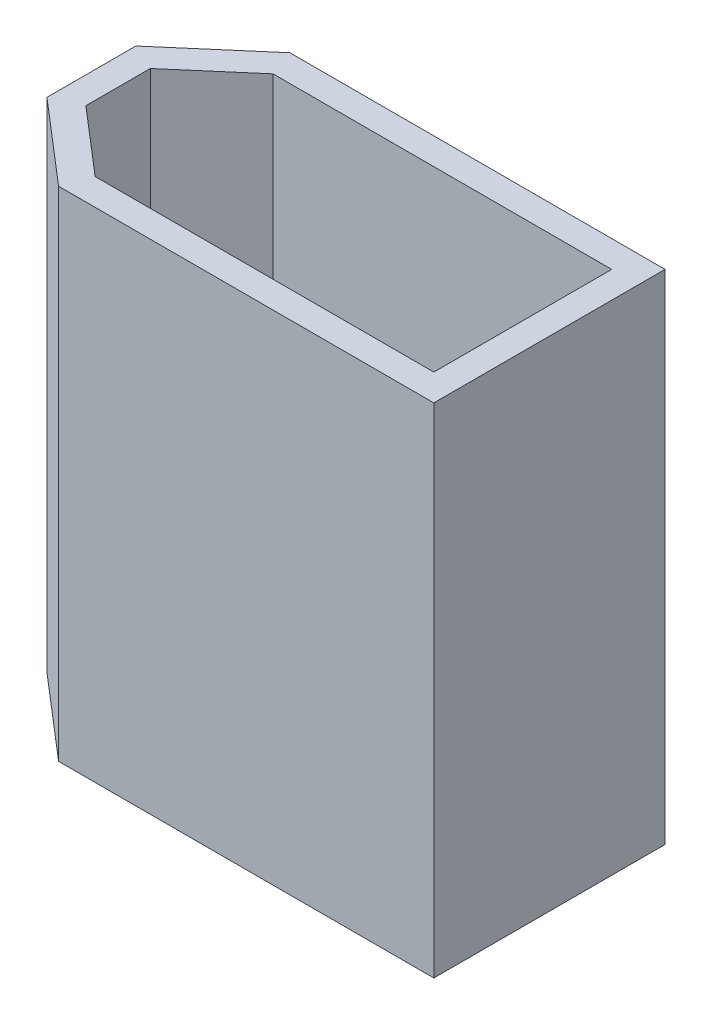
SolidWorks part; units mm, degrees
ref_plane "Front Plane" through (0, 0, 0) normal (0, 0, 1) x (1, 0, 0)
ref_plane "Top Plane" through (0, 0, 0) normal (0, 1, 0) x (1, 0, 0)
ref_plane "Right Plane" through (0, 0, 0) normal (1, 0, 0) x (0, 0, -1)
sketch "Sketch1" plane through (0, 0, 0) normal (0, 1, 0) x (1, 0, 0)
  line L0 (-3.2881, 2.6) -> (-5.15, 1)
  line L1 (5.15, -2.6) -> (-3.2881, -2.6)
  line L2 (5.15, -2.6) -> (5.15, 2.6)
  line L3 (5.15, 2.6) -> (-3.2881, 2.6)
  line L4 (-5.15, -1) -> (-5.15, 1)
  line L5 (5.15, -2.6) -> (-5.15, 2.6) construction
  line L6 (5.15, 2.6) -> (-5.15, -2.6) construction
  line L7 (-3.2881, -2.6) -> (-5.15, -1)
  line L8 (-5.15, 1) -> (-5.15, -1) construction
  line L9 (-3.2881, 2.6) -> (-5.15, 2.6) construction
  line L10 (-5.15, 2.6) -> (-5.15, 1) construction
  line L11 (-3.2881, -2.6) -> (-5.15, -2.6) construction
  line L12 (-5.15, -2.6) -> (-5.15, -1) construction
  line L13 (4.55, 2) -> (-3.0657, 2)
  line L14 (-3.0657, 2) -> (-4.55, 0.7245)
  line L15 (-4.55, -0.7245) -> (-4.55, 0.7245)
  line L16 (-3.0657, -2) -> (-4.55, -0.7245)
  line L17 (4.55, -2) -> (-3.0657, -2)
  line L18 (4.55, -2) -> (4.55, 2)
  point P0 (0, 0)
  point P10 (-5.15, 0)
  dimension "D1" = 10.3
  dimension "D2" = 5.2
  dimension "D3" = 2.455
  dimension "D4" = 2
  dimension "D5" = 0.6
extrude "Boss-Extrude1" add sketch "Sketch1" along normal blind 11.2
